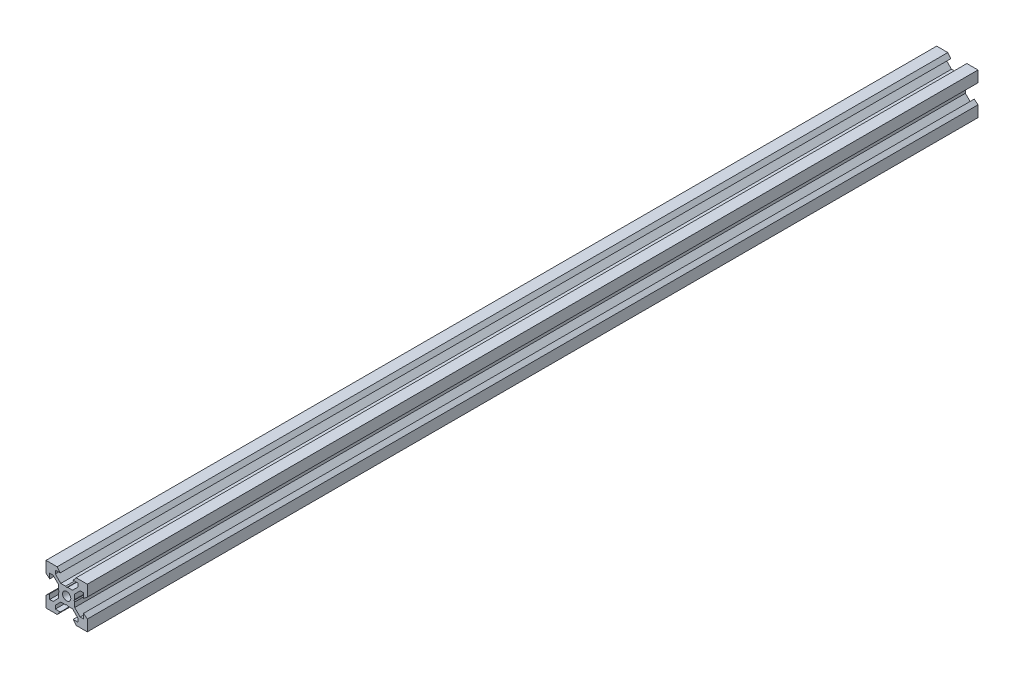
SolidWorks part; units mm, degrees
ref_plane "Front Plane" through (0, 0, 0) normal (0, 0, 1) x (1, 0, 0)
ref_plane "Top Plane" through (0, 0, 0) normal (0, 1, 0) x (1, 0, 0)
ref_plane "Right Plane" through (0, 0, 0) normal (1, 0, 0) x (0, 0, -1)
sketch "Sketch1" plane through (0, 0, 0) normal (0, 0, 1) x (1, 0, 0)
  line L0 (10, 10) -> (4.6104, 10) construction
  line L1 (10, 10) -> (10, 4.6104) construction
  line L2 (10, -10) -> (10, -4.6104) construction
  line L3 (10, -10) -> (4.6104, -10) construction
  line L4 (10, 10) -> (10, 4.6104)
  line L5 (6.5607, 5.5) -> (8.2, 5.5)
  line L6 (5.5, 8.2) -> (5.5, 6.5607)
  line L7 (10, 10) -> (4.6104, 10)
  line L8 (10, 10) -> (10, 4.6104)
  line L9 (6.5607, 5.5) -> (3.9, 2.8393)
  line L10 (5.5, 6.5607) -> (2.8393, 3.9)
  line L11 (10, 4.6104) -> (8.2, 3.1)
  line L12 (4.6104, 10) -> (3.1, 8.2)
  line L13 (8.2, 3.1) -> (8.2, 5.5)
  line L14 (3.1, 8.2) -> (5.5, 8.2)
  line L15 (-6.5607, 5.5) -> (-8.2, 5.5)
  line L16 (6.5607, -5.5) -> (8.2, -5.5)
  line L17 (3.1, -8.2) -> (5.5, -8.2)
  line L18 (8.2, -3.1) -> (8.2, -5.5)
  line L19 (4.6104, -10) -> (3.1, -8.2)
  line L20 (10, -4.6104) -> (8.2, -3.1)
  line L21 (0.5196, -3.9) -> (0, -3.6)
  line L22 (0.5196, 3.9) -> (0, 3.6)
  line L23 (3.6, 0) -> (3.9, -0.5196)
  line L24 (3.9, 0.5196) -> (3.6, 0)
  line L25 (3.9, 0.5196) -> (3.9, 2.8393)
  line L26 (2.8393, 3.9) -> (0.5196, 3.9)
  line L27 (3.9, -2.8393) -> (3.9, -0.5196)
  line L28 (2.8393, -3.9) -> (0.5196, -3.9)
  line L29 (5.5, -6.5607) -> (2.8393, -3.9)
  line L30 (6.5607, -5.5) -> (3.9, -2.8393)
  line L31 (10, -10) -> (10, -4.6104)
  line L32 (10, -10) -> (4.6104, -10)
  line L33 (5.5, -8.2) -> (5.5, -6.5607)
  line L34 (-6.5607, -5.5) -> (-8.2, -5.5)
  line L35 (10, -10) -> (10, -4.6104)
  line L36 (0, 0) -> (0, 8.2) construction
  line L37 (-10, -10) -> (-4.6104, -10) construction
  line L38 (-10, -10) -> (-10, -4.6104) construction
  line L39 (-10, 10) -> (-10, 4.6104) construction
  line L40 (-10, 10) -> (-4.6104, 10) construction
  line L41 (-10, -10) -> (-10, -4.6104)
  line L43 (-5.5, -8.2) -> (-5.5, -6.5607)
  line L44 (-10, -10) -> (-4.6104, -10)
  line L45 (-10, -10) -> (-10, -4.6104)
  line L46 (-6.5607, -5.5) -> (-3.9, -2.8393)
  line L47 (-5.5, -6.5607) -> (-2.8393, -3.9)
  line L48 (-2.8393, -3.9) -> (-0.5196, -3.9)
  line L49 (-3.9, -2.8393) -> (-3.9, -0.5196)
  line L50 (-2.8393, 3.9) -> (-0.5196, 3.9)
  line L51 (-3.9, 0.5196) -> (-3.9, 2.8393)
  line L52 (-3.9, 0.5196) -> (-3.6, 0)
  line L53 (-3.6, 0) -> (-3.9, -0.5196)
  line L54 (-0.5196, 3.9) -> (0, 3.6)
  line L55 (-0.5196, -3.9) -> (0, -3.6)
  line L56 (-10, -4.6104) -> (-8.2, -3.1)
  line L57 (-4.6104, -10) -> (-3.1, -8.2)
  line L58 (-8.2, -3.1) -> (-8.2, -5.5)
  line L59 (-3.1, -8.2) -> (-5.5, -8.2)
  line L60 (-10, -10) -> (10, -10) construction
  line L61 (-10, -10) -> (-10, 10) construction
  line L62 (-3.1, 8.2) -> (-5.5, 8.2)
  line L63 (-8.2, 3.1) -> (-8.2, 5.5)
  line L64 (-4.6104, 10) -> (-3.1, 8.2)
  line L65 (-10, 4.6104) -> (-8.2, 3.1)
  line L66 (-5.5, 6.5607) -> (-2.8393, 3.9)
  line L67 (-6.5607, 5.5) -> (-3.9, 2.8393)
  line L68 (-10, 10) -> (-10, 4.6104)
  line L69 (-10, 10) -> (-4.6104, 10)
  line L70 (-5.5, 8.2) -> (-5.5, 6.5607)
  line L71 (-10, 10) -> (10, 10) construction
  line L72 (-10, 10) -> (-10, 4.6104)
  line L73 (10, -10) -> (10, 10) construction
  line L74 (-10, -10) -> (10, 10) construction
  line L75 (-10, 10) -> (10, -10) construction
  circle A0 centre (0, 0) radius 2
  dimension "D7" = 4
  dimension "D1" = 20
  dimension "D2" = 5.3896
  dimension "D3" = 4.5
  dimension "D4" = 50
  dimension "D5" = 1.8
  dimension "D6" = 1.5104
  dimension "D8" = 5.5
  dimension "D9" = 120
  dimension "D10" = 0.3
  dimension "D11" = 2.3197
  dimension "D12" = 7.8
  dimension "D13" = 7.8
  dimension "D14" = 1.5
  dimension "D15" = 2.6607
extrude "Boss-Extrude1" add sketch "Sketch1" along normal mid plane 431.2 contours L70 L62 L64 L69 L68 L65 L63 L15 L67 L51 L52 L53 L49 L46 L34 L58 L56 L41 L44 L57 L59 L43 L47 L48 L55 L21 L28 L29 L33 L17 L19 L32 L31 L20 L18 L16 L30 L27 L23 L24 L25 L9 L5 L13 L11 L4 L7 L12 L14 L6 L10
